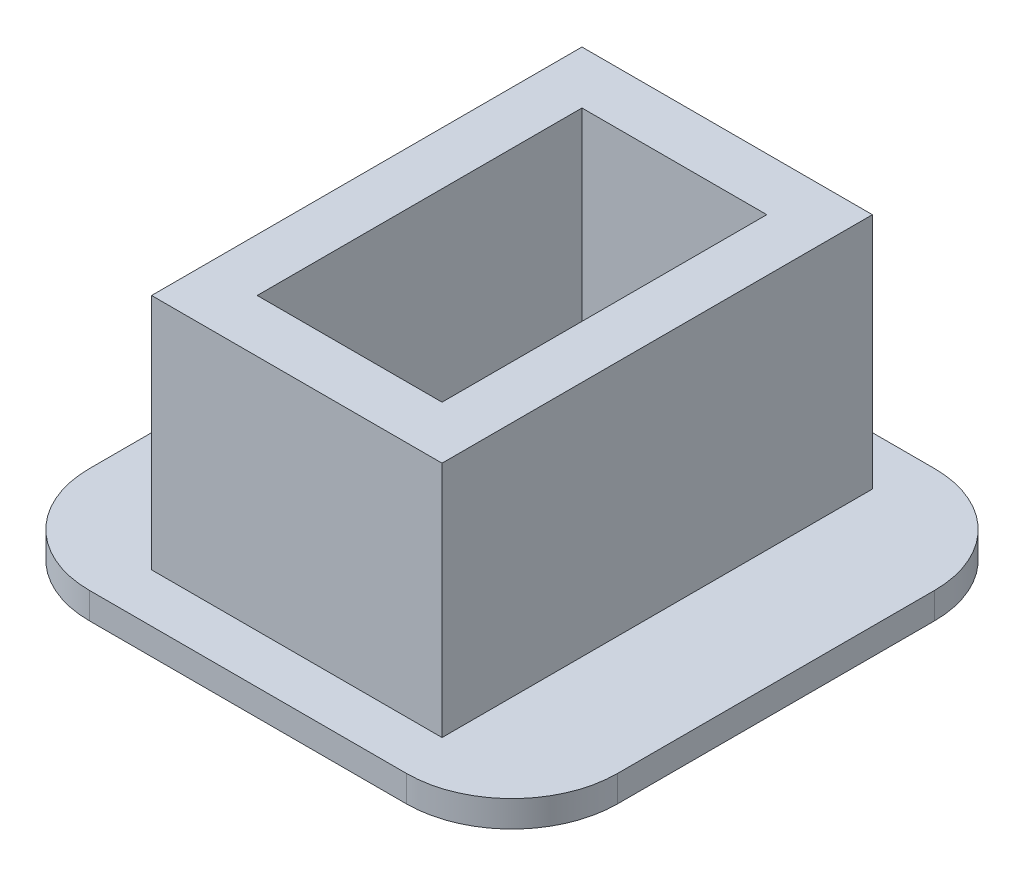
SolidWorks part; units mm, degrees
ref_plane "Front Plane" through (0, 0, 0) normal (0, 0, 1) x (1, 0, 0)
ref_plane "Top Plane" through (0, 0, 0) normal (0, 1, 0) x (1, 0, 0)
ref_plane "Right Plane" through (0, 0, 0) normal (1, 0, 0) x (0, 0, -1)
sketch "Sketch1" plane through (0, 0, 0) normal (0, 1, 0) x (1, 0, 0)
  line L0 (7, 12.3) -> (-7, 12.3)
  line L1 (11, 16.3) -> (-11, 16.3)
  line L2 (-11, 16.3) -> (-11, -16.3)
  line L3 (11, -16.3) -> (-11, -16.3)
  line L4 (11, 16.3) -> (11, -16.3)
  line L5 (-7, 12.3) -> (-7, -12.3)
  line L6 (7, -12.3) -> (-7, -12.3)
  line L7 (7, 12.3) -> (7, -12.3)
  line L8 (-11, 16.3) -> (11, -16.3) construction
  point P0 (0, 0)
extrude "Boss-Extrude1" add sketch "Sketch1" along normal blind 18
sketch "Sketch2" plane through (0, 18, 0) normal (0, 1, 0) x (1, 0, 0)
  line L0 (0, -14) -> (0, 14) construction
  circle A0 centre (0, 14) radius 1 construction
  circle A1 centre (0, -14) radius 1 construction
sketch "Sketch3" plane through (0, 0, 0) normal (0, -1, 0) x (1, 0, 0)
  line L1 (-20, -20) -> (20, -20)
  line L2 (-20, -20) -> (-20, 20)
  line L3 (-20, 20) -> (20, 20)
  line L4 (20, -20) -> (20, 20)
  line L5 (-20, -20) -> (20, 20) construction
  line L6 (-20, 20) -> (20, -20) construction
  point P0 (0, 0)
  dimension "D1" = 40
  dimension "D2" = 40
extrude "Boss-Extrude2" add sketch "Sketch3" along normal blind 2
fillet "Fillet1" radius 8 4 edges at (-20, -1, 20) (20, -1, 20) (-20, -1, -20) (20, -1, -20)
